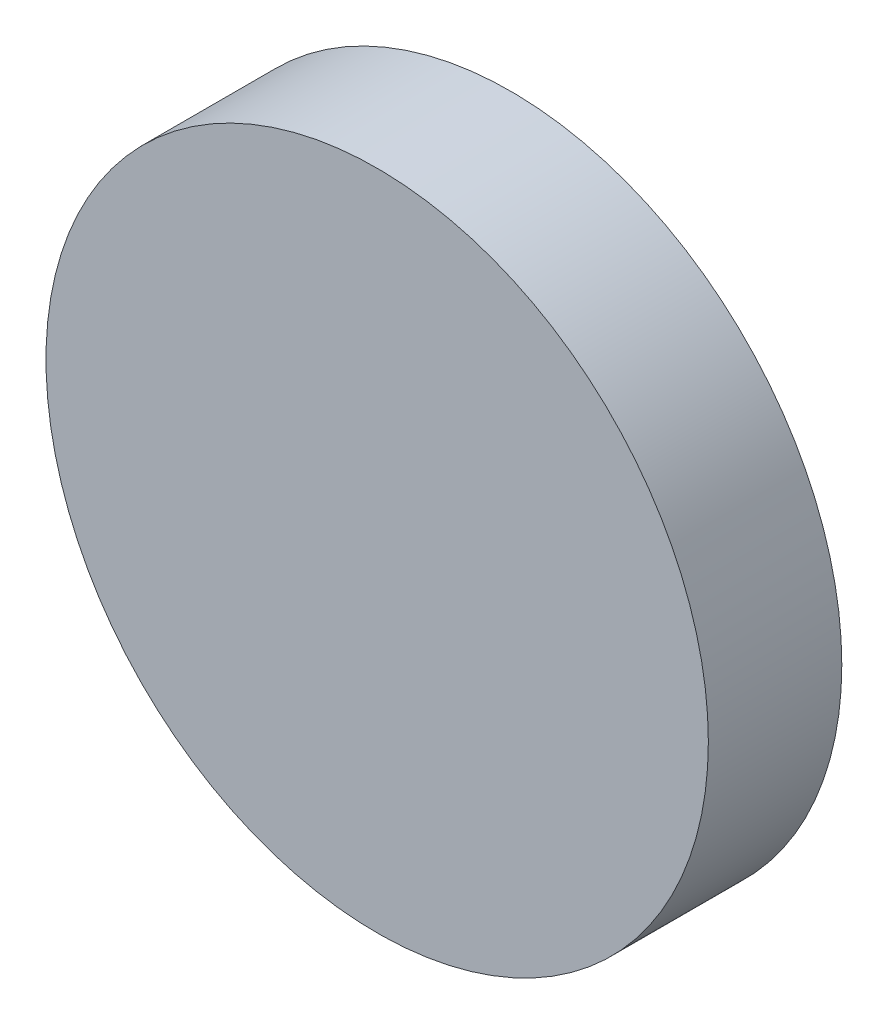
SolidWorks part; units mm, degrees
material "Boron"
ref_plane "Front" through (0, 0, 0) normal (0, 0, 1) x (1, 0, 0)
ref_plane "Top" through (0, 0, 0) normal (0, 1, 0) x (1, 0, 0)
ref_plane "Right" through (0, 0, 0) normal (1, 0, 0) x (0, 0, -1)
sketch "Sketch1" plane through (0, 0, 0) normal (0, 0, 1) x (1, 0, 0)
  circle A0 centre (0, 0) radius 133.5
extrude "Boss-Extrude1" add sketch "Sketch1" along normal blind 53.8
